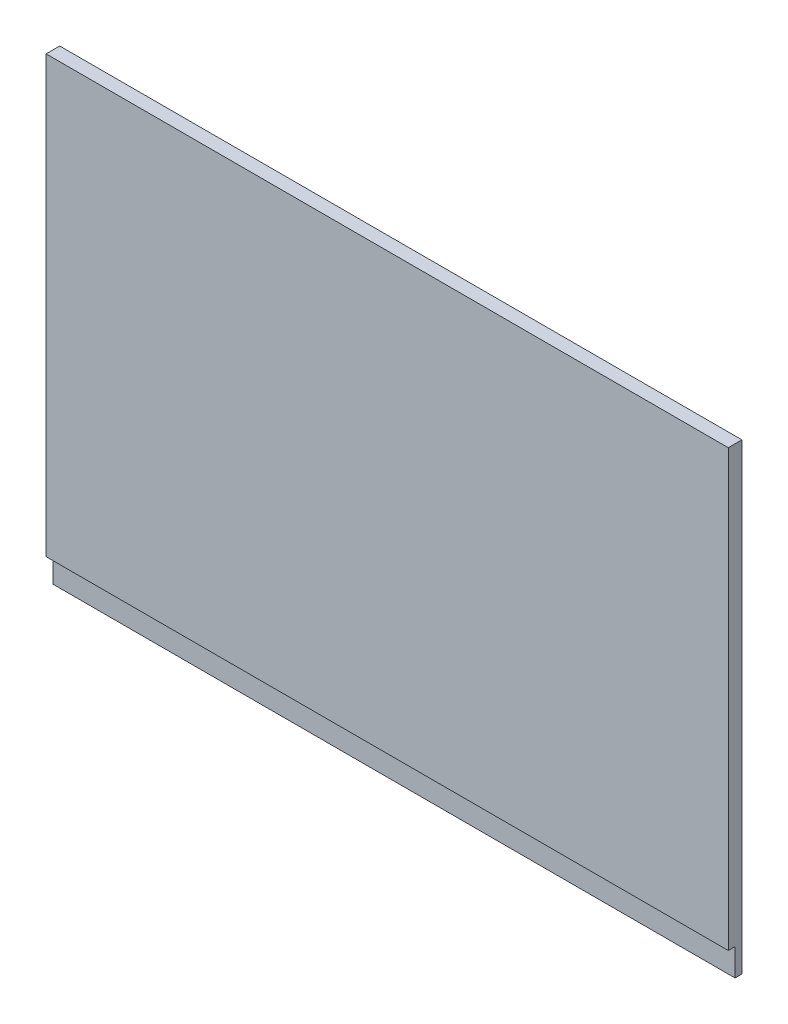
SolidWorks part; units mm, degrees
ref_plane "Front Plane" through (0, 0, 0) normal (0, 0, 1) x (1, 0, 0)
ref_plane "Top Plane" through (0, 0, 0) normal (0, 1, 0) x (1, 0, 0)
ref_plane "Right Plane" through (0, 0, 0) normal (1, 0, 0) x (0, 0, -1)
sketch "Sketch1" plane through (0, 0, 0) normal (0, 0, 1) x (1, 0, 0)
  line L1 (0, 0) -> (-159.1564, 0)
  line L2 (0, 0) -> (0, 107.95)
  line L3 (0, 107.95) -> (-159.1564, 107.95)
  line L4 (-159.1564, 0) -> (-159.1564, 107.95)
  dimension "D1" = 107.95
  dimension "D2" = 159.1564
extrude "Boss-Extrude1" add sketch "Sketch1" along normal blind 3.175
sketch "Sketch2" plane through (0, 0, 3.175) normal (0, 0, 1) x (1, 0, 0)
  line L0 (0, 0) -> (0, 107.95) construction
  line L1 (-159.1564, 0) -> (0, 0)
  line L2 (-159.1564, 0) -> (-159.1564, 6.35)
  line L3 (-159.1564, 6.35) -> (0, 6.35)
  line L4 (0, 0) -> (0, 6.35)
  dimension "D1" = 6.35
extrude "Cut-Extrude1" cut sketch "Sketch2" against normal blind 1.5875
